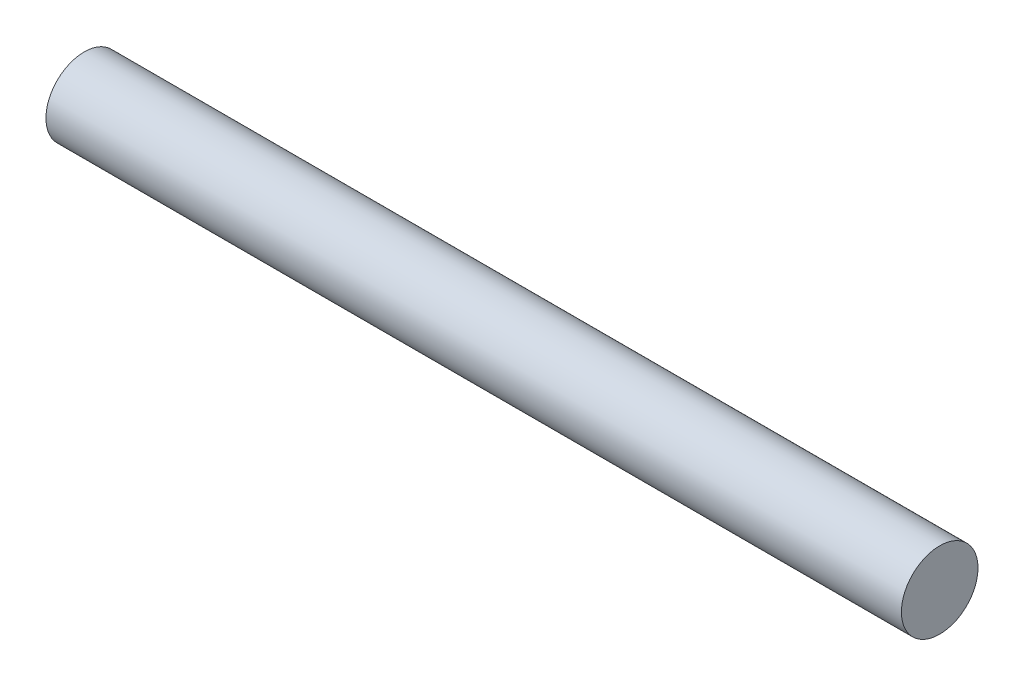
SolidWorks part; units mm, degrees
material "Plain Carbon Steel"
ref_plane "Front Plane" through (0, 0, 0) normal (0, 0, 1) x (1, 0, 0)
ref_plane "Top Plane" through (0, 0, 0) normal (0, 1, 0) x (1, 0, 0)
ref_plane "Right Plane" through (0, 0, 0) normal (1, 0, 0) x (0, 0, -1)
sketch "Sketch1" plane through (0, 0, 0) normal (1, 0, 0) x (0, 0, -1)
  circle A0 centre (0, 0) radius 9.525
extrude "Boss-Extrude1" add sketch "Sketch1" along normal mid plane 212.725
